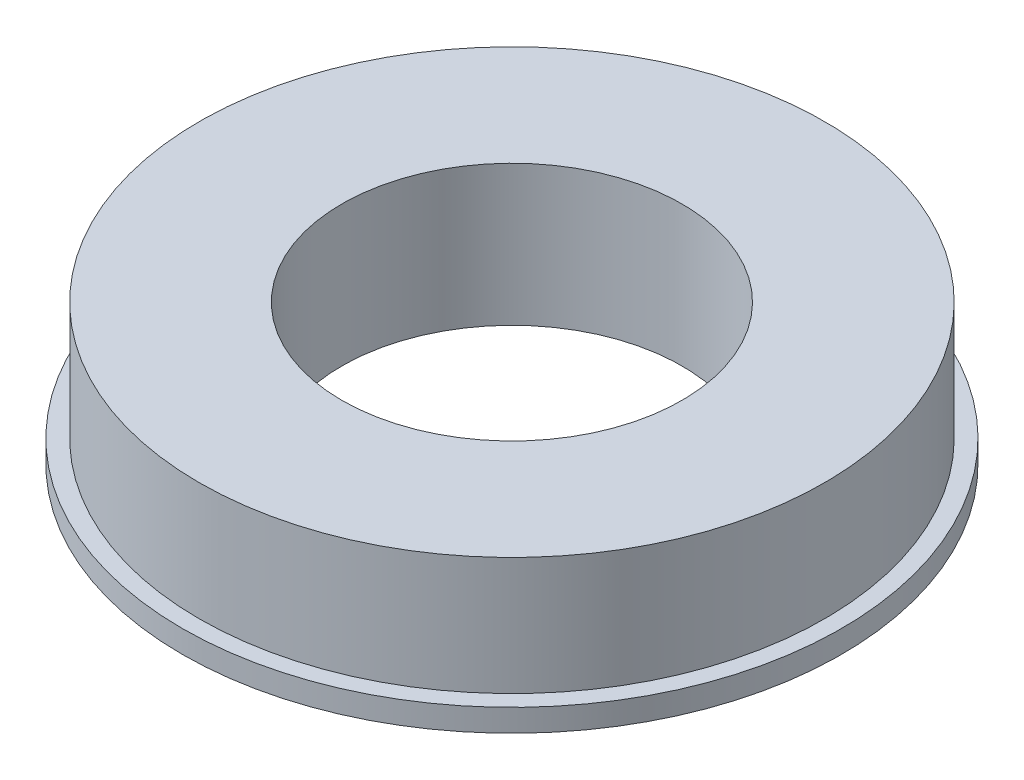
SolidWorks part; units mm, degrees
ref_plane "Front Plane" through (0, 0, 0) normal (0, 0, 1) x (1, 0, 0)
ref_plane "Top Plane" through (0, 0, 0) normal (0, 1, 0) x (1, 0, 0)
ref_plane "Right Plane" through (0, 0, 0) normal (1, 0, 0) x (0, 0, -1)
sketch "Sketch1" plane through (0, 0, 0) normal (0, 1, 0) x (1, 0, 0)
  circle A0 centre (0, 0) radius 27.85
  circle A1 centre (0, 0) radius 15.15
  dimension "D1" = 55.7
  dimension "D2" = 30.3
extrude "Boss-Extrude1" add sketch "Sketch1" along normal blind 12.5
sketch "Sketch3" plane through (0, 12.5, 0) normal (0, 1, 0) x (1, 0, 0)
  circle A0 centre (0, 0) radius 29.35
  circle A1 centre (0, 0) radius 27.85
  circle A2 centre (0, 0) radius 27.85 construction
  dimension "D1" = 58.7
extrude "Boss-Extrude3" add sketch "Sketch3" along normal blind 2 from offset 12.5
